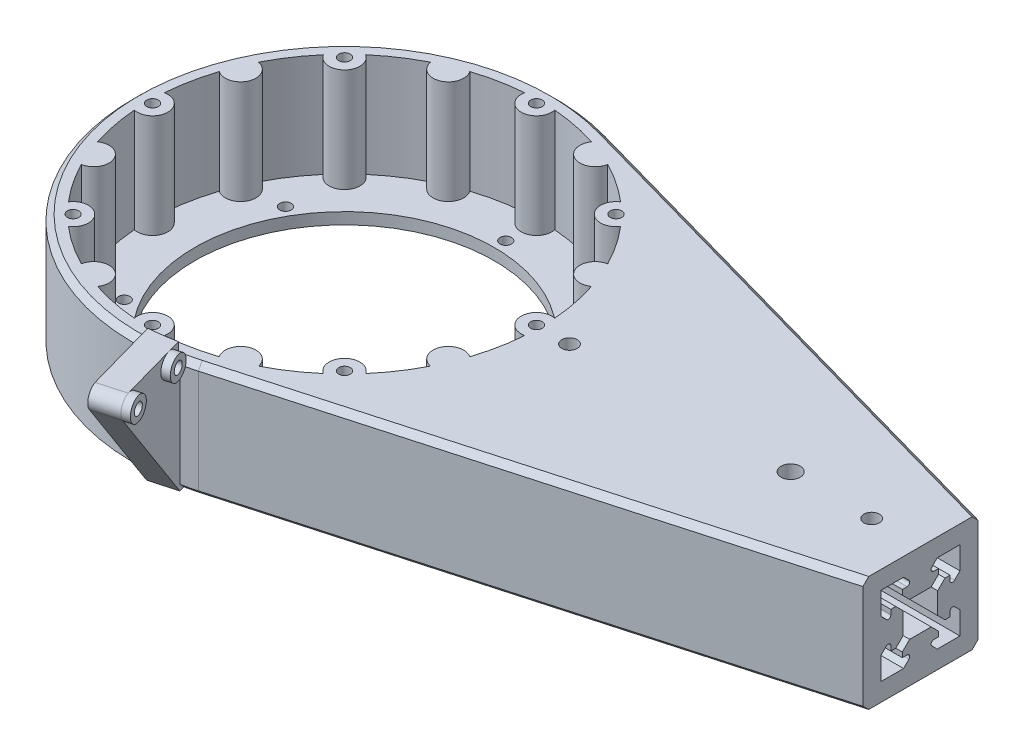
SolidWorks part; units mm, degrees
ref_plane "Front Plane" through (0, 0, 0) normal (0, 0, 1) x (1, 0, 0)
ref_plane "Top Plane" through (0, 0, 0) normal (0, 1, 0) x (1, 0, 0)
ref_plane "Right Plane" through (0, 0, 0) normal (1, 0, 0) x (0, 0, -1)
sketch "Sketch1" plane through (0, 0, 0) normal (0, 1, 0) x (1, 0, 0)
  circle A0 centre (0, 0) radius 39
  circle A1 centre (0, 0) radius 55
  circle A2 centre (0, 50) radius 1.5
  circle A3 centre (35.3553, 35.3553) radius 1.5
  circle A4 centre (50, 0) radius 1.5
  circle A5 centre (35.3553, -35.3553) radius 1.5
  circle A6 centre (0, -50) radius 1.5
  circle A7 centre (-35.3553, -35.3553) radius 1.5
  circle A8 centre (-50, 0) radius 1.5
  circle A9 centre (-35.3553, 35.3553) radius 1.5
  circle A18 centre (0, 42) radius 1.5
  circle A19 centre (36.3731, 21) radius 1.5
  circle A20 centre (36.3731, -21) radius 1.5
  circle A21 centre (0, -42) radius 1.5
  circle A22 centre (-36.3731, -21) radius 1.5
  circle A23 centre (-36.3731, 21) radius 1.5
  point P22 (0, 0)
  point P35 (0, 0)
  point P39 (0, 0)
  dimension "D1" = 110
  dimension "D2" = 78
  dimension "D3" = 3
  dimension "D6" = 42
  dimension "D7" = 3
  dimension "D4" = 50
  dimension "D5" = 8
  dimension "D8" = 6
extrude "Boss-Extrude1" add sketch "Sketch1" along normal blind 3
sketch "Sketch2" plane through (0, 3, 0) normal (0, 1, 0) x (1, 0, 0)
  arc A0 (-3.9086, 50.85) -> (3.9086, 50.85) centre (0, 50) ccw
  arc A1 (15.8483, 48.475) -> (23.0706, 45.4835) centre (19.1342, 46.194) ccw
  arc A2 (33.1926, 38.7202) -> (38.7202, 33.1926) centre (35.3553, 35.3553) ccw
  arc A3 (45.4835, 23.0706) -> (48.475, 15.8483) centre (46.194, 19.1342) ccw
  arc A4 (50.85, 3.9086) -> (50.85, -3.9086) centre (50, 0) ccw
  arc A5 (48.475, -15.8483) -> (45.4835, -23.0706) centre (46.194, -19.1342) ccw
  arc A6 (38.7202, -33.1926) -> (33.1926, -38.7202) centre (35.3553, -35.3553) ccw
  arc A7 (23.0706, -45.4835) -> (15.8483, -48.475) centre (19.1342, -46.194) ccw
  arc A8 (3.9086, -50.85) -> (-3.9086, -50.85) centre (0, -50) ccw
  arc A9 (-15.8483, -48.475) -> (-23.0706, -45.4835) centre (-19.1342, -46.194) ccw
  arc A10 (-33.1926, -38.7202) -> (-38.7202, -33.1926) centre (-35.3553, -35.3553) ccw
  arc A11 (-45.4835, -23.0706) -> (-48.475, -15.8483) centre (-46.194, -19.1342) ccw
  arc A12 (-50.85, -3.9086) -> (-50.85, 3.9086) centre (-50, 0) ccw
  arc A13 (-48.475, 15.8483) -> (-45.4835, 23.0706) centre (-46.194, 19.1342) ccw
  arc A14 (-38.7202, 33.1926) -> (-33.1926, 38.7202) centre (-35.3553, 35.3553) ccw
  arc A15 (-23.0706, 45.4835) -> (-15.8483, 48.475) centre (-19.1342, 46.194) ccw
  arc A16 (-48.475, 15.8483) -> (-50.85, 3.9086) centre (0, 0) ccw
  arc A17 (-50.85, -3.9086) -> (-48.475, -15.8483) centre (0, 0) ccw
  arc A18 (-45.4835, -23.0706) -> (-38.7202, -33.1926) centre (0, 0) ccw
  arc A19 (-33.1926, -38.7202) -> (-23.0706, -45.4835) centre (0, 0) ccw
  arc A20 (-15.8483, -48.475) -> (-3.9086, -50.85) centre (0, 0) ccw
  arc A21 (3.9086, -50.85) -> (15.8483, -48.475) centre (0, 0) ccw
  arc A22 (23.0706, -45.4835) -> (33.1926, -38.7202) centre (0, 0) ccw
  arc A23 (38.7202, -33.1926) -> (45.4835, -23.0706) centre (0, 0) ccw
  arc A24 (48.475, -15.8483) -> (50.85, -3.9086) centre (0, 0) ccw
  arc A25 (50.85, 3.9086) -> (48.475, 15.8483) centre (0, 0) ccw
  arc A26 (45.4835, 23.0706) -> (38.7202, 33.1926) centre (0, 0) ccw
  arc A27 (33.1926, 38.7202) -> (23.0706, 45.4835) centre (0, 0) ccw
  arc A28 (15.8483, 48.475) -> (3.9086, 50.85) centre (0, 0) ccw
  arc A29 (-3.9086, 50.85) -> (-15.8483, 48.475) centre (0, 0) ccw
  arc A30 (-23.0706, 45.4835) -> (-33.1926, 38.7202) centre (0, 0) ccw
  arc A31 (-38.7202, 33.1926) -> (-45.4835, 23.0706) centre (0, 0) ccw
  circle A32 centre (0, 0) radius 55 construction
  circle A33 centre (0, 0) radius 55
  circle A34 centre (-35.3553, 35.3553) radius 1.5 construction
  circle A35 centre (-50, 0) radius 1.5 construction
  circle A36 centre (-35.3553, -35.3553) radius 1.5 construction
  circle A37 centre (0, -50) radius 1.5 construction
  circle A38 centre (35.3553, -35.3553) radius 1.5 construction
  circle A39 centre (50, 0) radius 1.5 construction
  circle A40 centre (35.3553, 35.3553) radius 1.5 construction
  circle A41 centre (0, 50) radius 1.5 construction
  circle A42 centre (-35.3553, 35.3553) radius 1.5
  circle A43 centre (-50, 0) radius 1.5
  circle A44 centre (-35.3553, -35.3553) radius 1.5
  circle A45 centre (0, -50) radius 1.5
  circle A46 centre (35.3553, -35.3553) radius 1.5
  circle A47 centre (50, 0) radius 1.5
  circle A48 centre (35.3553, 35.3553) radius 1.5
  circle A49 centre (0, 50) radius 1.5
  point P35 (0, 0)
  dimension "D1" = 8
  dimension "D4" = 102
  dimension "D2" = 50
  dimension "D3" = 16
extrude "Boss-Extrude3" add sketch "Sketch2" along normal blind 27
sketch "Sketch3" plane through (0, 30, 0) normal (0, 1, 0) x (1, 0, 0)
  line L0 (0, 0) -> (150, 0) construction
  line L1 (14.8715, 52.9513) -> (150, 15)
  line L3 (14.8715, -52.9513) -> (150, -15)
  line L4 (150, 15) -> (150, -15)
  circle A0 centre (0, 0) radius 55 construction
  arc A1 (14.8715, -52.9513) -> (55, 0) centre (0, 0) ccw
  circle A2 centre (58.6, 0) radius 2
  circle A3 centre (116.2, 0) radius 2.5
  circle A4 centre (137.3, 0) radius 2
  arc A5 (14.8715, -52.9513) -> (14.8715, 52.9513) centre (0, 0) ccw
  point P12 (150, 0)
  dimension "D1" = 150
  dimension "D4" = 4
  dimension "D2" = 5
  dimension "D3" = 30
  dimension "D5" = 57.6
  dimension "D6" = 21.1
  dimension "D7" = 91.4
extrude "Boss-Extrude4" add sketch "Sketch3" along normal blind 30 from surface at -30
sketch "Sketch4" plane through (150, 0, 0) normal (1, 0, 0) x (0, 0, -1)
  line L120 (2.8029, 19.5) -> (-2.8029, 19.5)
  line L121 (-2.8029, 19.5) -> (-4.7101, 21.4071)
  line L122 (-4.7101, 21.4071) -> (-4.7101, 22.7)
  line L123 (-4.7101, 22.7) -> (-3.4828, 22.7)
  line L124 (-2.9879, 23.895) -> (-4.3879, 25.295)
  line L125 (-10.295, 19.3879) -> (-8.895, 17.9879)
  line L126 (-7.7, 18.4828) -> (-7.7, 19.7101)
  line L127 (-7.7, 19.7101) -> (-6.4071, 19.7101)
  line L128 (-6.4071, 19.7101) -> (-4.5, 17.8029)
  line L129 (-4.5, 17.8029) -> (-4.5, 12.1971)
  line L130 (-4.5, 12.1971) -> (-6.4071, 10.2899)
  line L131 (-6.4071, 10.2899) -> (-7.7, 10.2899)
  line L132 (-7.7, 10.2899) -> (-7.7, 11.5172)
  line L133 (-8.895, 12.0121) -> (-10.295, 10.6121)
  line L134 (-4.3879, 4.705) -> (-2.9879, 6.105)
  line L135 (-3.4828, 7.3) -> (-4.7101, 7.3)
  line L136 (-4.7101, 7.3) -> (-4.7101, 8.5929)
  line L137 (-4.7101, 8.5929) -> (-2.8029, 10.5)
  line L138 (-2.8029, 10.5) -> (2.8029, 10.5)
  line L146 (-4.3879, 4.705) -> (-10.295, 4.705)
  line L147 (-10.295, 4.705) -> (-10.295, 10.6121)
  line L148 (-10.295, 19.3879) -> (-10.295, 25.295)
  line L149 (-10.295, 25.295) -> (-4.3879, 25.295)
  line L158 (-15, 30) -> (-15, 0) construction
  line L161 (10.295, 25.295) -> (4.3879, 25.295)
  line L162 (10.295, 19.3879) -> (10.295, 25.295)
  line L163 (10.295, 4.705) -> (10.295, 10.6121)
  line L164 (4.3879, 4.705) -> (10.295, 4.705)
  line L165 (4.7101, 8.5929) -> (2.8029, 10.5)
  line L166 (4.7101, 7.3) -> (4.7101, 8.5929)
  line L167 (3.4828, 7.3) -> (4.7101, 7.3)
  line L168 (4.3879, 4.705) -> (2.9879, 6.105)
  line L169 (8.895, 12.0121) -> (10.295, 10.6121)
  line L170 (7.7, 10.2899) -> (7.7, 11.5172)
  line L171 (6.4071, 10.2899) -> (7.7, 10.2899)
  line L172 (4.5, 12.1971) -> (6.4071, 10.2899)
  line L173 (4.5, 17.8029) -> (4.5, 12.1971)
  line L174 (6.4071, 19.7101) -> (4.5, 17.8029)
  line L175 (7.7, 19.7101) -> (6.4071, 19.7101)
  line L176 (7.7, 18.4828) -> (7.7, 19.7101)
  line L177 (10.295, 19.3879) -> (8.895, 17.9879)
  line L178 (2.9879, 23.895) -> (4.3879, 25.295)
  line L179 (4.7101, 22.7) -> (3.4828, 22.7)
  line L180 (4.7101, 21.4071) -> (4.7101, 22.7)
  line L181 (2.8029, 19.5) -> (4.7101, 21.4071)
  arc A40 (2.9879, 6.105) -> (3.4828, 7.3) centre (3.4828, 6.6) cw
  arc A42 (-3.4828, 22.7) -> (-2.9879, 23.895) centre (-3.4828, 23.4) ccw
  arc A43 (7.7, 11.5172) -> (8.895, 12.0121) centre (8.4, 11.5172) cw
  arc A44 (8.895, 17.9879) -> (7.7, 18.4828) centre (8.4, 18.4828) cw
  arc A45 (-8.895, 17.9879) -> (-7.7, 18.4828) centre (-8.4, 18.4828) ccw
  arc A46 (-7.7, 11.5172) -> (-8.895, 12.0121) centre (-8.4, 11.5172) ccw
  arc A47 (3.4828, 22.7) -> (2.9879, 23.895) centre (3.4828, 23.4) cw
  arc A49 (-2.9879, 6.105) -> (-3.4828, 7.3) centre (-3.4828, 6.6) ccw
  point P0 (0, 19.5)
  point P15 (-4.5, 15)
  dimension "D22" = 0.7
  dimension "D31" = 0.7
  dimension "D46" = 0.7
  dimension "D8" = 5.6059
  dimension "D9" = 2.6971
  dimension "D10" = 1.2929
  dimension "D11" = 2.595
  dimension "D13" = 135
  dimension "D21" = 1.2934
  dimension "D23" = 1.9799
  dimension "D24" = 135
  dimension "D25" = 1.2272
  dimension "D26" = 5.6059
  dimension "D27" = 2.6971
  dimension "D28" = 1.2929
  dimension "D29" = 1.2272
  dimension "D30" = 1.2934
  dimension "D32" = 1.9799
  dimension "D33" = 225
  dimension "D34" = 5.9071
  dimension "D35" = 135
  dimension "D36" = 90
  dimension "D37" = 135
  dimension "D38" = 2.595
  dimension "D39" = 135
  dimension "D40" = 135
  dimension "D41" = 1.2934
  dimension "D42" = 5.9071
  dimension "D43" = 1.9799
  dimension "D44" = 135
  dimension "D45" = 1.2934
  dimension "D47" = 1.2272
  dimension "D48" = 90
  dimension "D49" = 135
  dimension "D50" = 1.2929
  dimension "D51" = 2.595
  dimension "D52" = 2.6971
  dimension "D54" = 5.6059
  dimension "D64" = 5.9071
  dimension "D69" = 15
  dimension "D70" = 15
extrude "Cut-Extrude1" cut sketch "Sketch4" against normal blind 134
sketch "Sketch10" plane through (14.8715, 0, 52.9513) normal (0.2704, 0, 0.9628) x (0.9628, 0, -0.2704)
  line L1 (-11, 34) -> (-4, 34)
  line L2 (-11, 34) -> (-11, 0)
  line L3 (-11, 0) -> (-4, 0)
  line L4 (-4, 34) -> (-4, 0)
  line L6 (0, 30) -> (0, 0) construction
  line L8 (0, 0) -> (140.3567, 0) construction
  line L9 (28.6352, 30) -> (-55, 30) construction
  dimension "D1" = 7
  dimension "D2" = 11
  dimension "D3" = 4
extrude "Boss-Extrude7" add sketch "Sketch10" along normal blind 22 and the other way blind 2
sketch "Sketch11" plane through (-3.851, 0, 1.0816) normal (0.9628, 0, -0.2704) x (-0.2704, 0, -0.9628)
  line L0 (-77, 0) -> (-77, 34) construction
  line L1 (-77, 34) -> (-53, 34) construction
  line L2 (-54.8544, 0) -> (-76.4133, 29.2299)
  line L3 (-76.9987, 31.0099) -> (-77, 0)
  line L4 (-77, 0) -> (-54.8544, 0)
  line L5 (-76.9987, 31.0099) -> (-77, 34)
  line L6 (-77, 34) -> (-73.7728, 34)
  circle A0 centre (-74, 31.0099) radius 1.5
  circle A1 centre (-59, 31.0099) radius 1.5
  arc A2 (-73.7728, 34) -> (-76.4133, 29.2299) centre (-74, 31.0099) ccw
  line M6 (-77, 0) -> (-54.8544, 0)
  dimension "D2" = 3
  dimension "D5" = 5.9975
  dimension "D1" = 15
  dimension "D3" = 3
extrude "Cut-Extrude5" cut sketch "Sketch11" against normal blind 20 contours A2 L3 L2 M6 | A2 L6 L5 | A0 | A1
sketch "Sketch12" plane through (-3.851, 0, 1.0816) normal (0.9628, 0, -0.2704) x (-0.2704, 0, -0.9628)
  circle A0 centre (-74, 31.0099) radius 3
  circle A1 centre (-59, 31.0099) radius 3
  circle A2 centre (-59, 31.0099) radius 1.5 construction
  circle A3 centre (-74, 31.0099) radius 1.5 construction
  circle A4 centre (-59, 31.0099) radius 1.5
  circle A5 centre (-74, 31.0099) radius 1.5
  dimension "D1" = 1.5
extrude "Boss-Extrude10" add sketch "Sketch12" along normal blind 2
sketch "Sketch13" plane through (0, 30, 0) normal (0, 1, 0) x (1, 0, 0)
  circle A0 centre (0, 0) radius 55.5
  dimension "D1" = 111
extrude "Cut-Extrude6" cut sketch "Sketch13" along normal through all
chamfer "Chamfer1" distance 1.5 angle 45 8 edges at (82.4358, 0, 33.9756) (82.4358, 30, 33.9756) (-54.7215, 0, -5.528) (-54.7215, 30, -5.528) (12.9349, 30, 53.4573) (12.9349, 0, 53.4573) (82.4358, 0, -33.9756) (82.4358, 30, -33.9756)
